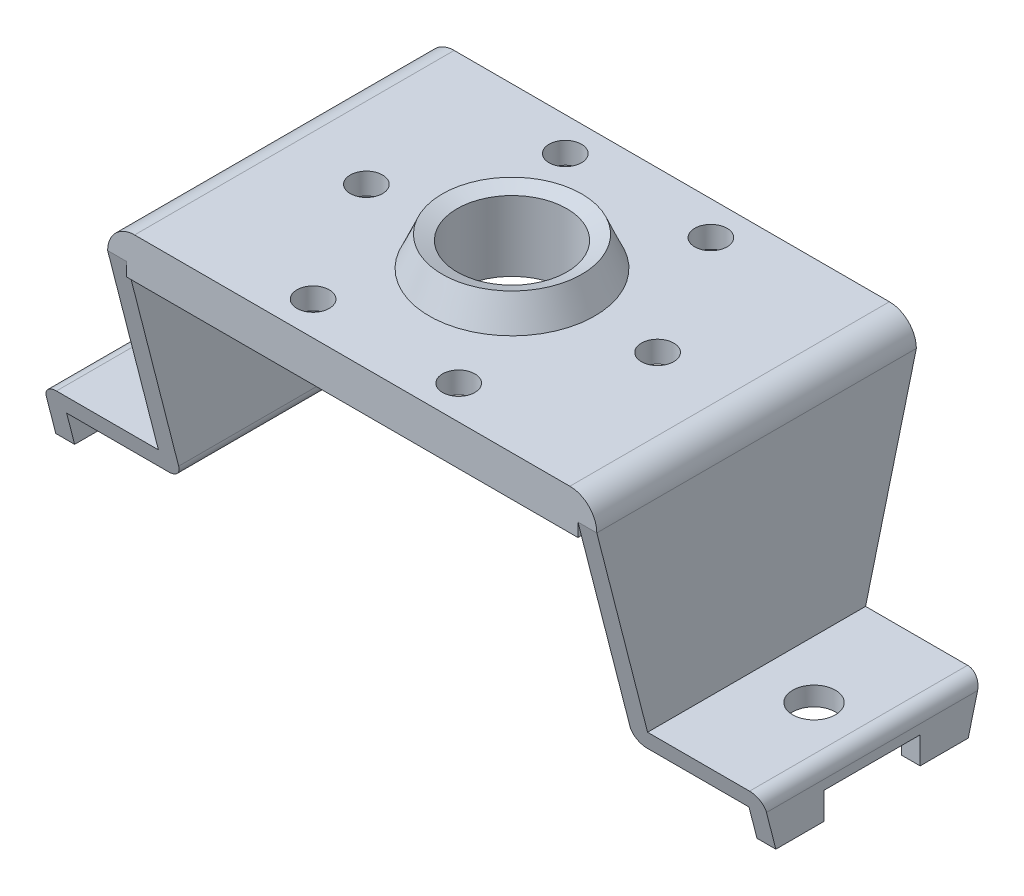
SolidWorks part; units mm, degrees
ref_plane "Front Plane" through (0, 0, 0) normal (0, 0, 1) x (1, 0, 0)
ref_plane "Top Plane" through (0, 0, 0) normal (0, 1, 0) x (1, 0, 0)
ref_plane "Right Plane" through (0, 0, 0) normal (1, 0, 0) x (0, 0, -1)
sketch "Sketch1" plane through (0, 0, 0) normal (0, 1, 0) x (1, 0, 0)
  line L1 (-17.9768, -15.0622) -> (17.9768, -15.0622)
  line L2 (-23.0568, -9.9822) -> (-23.0568, 9.9822)
  line L3 (-17.9768, 15.0622) -> (17.9768, 15.0622)
  line L4 (23.0569, -9.9822) -> (23.0569, 9.9822)
  line L5 (-23.0568, -15.0622) -> (23.0569, 15.0622) construction
  line L6 (-23.0568, 15.0622) -> (23.0569, -15.0622) construction
  arc A0 (-17.9768, -15.0622) -> (-23.0568, -9.9822) centre (-17.9768, -9.9822) cw
  arc A1 (17.9768, -15.0622) -> (23.0569, -9.9822) centre (17.9769, -9.9822) ccw
  arc A2 (17.9768, 15.0622) -> (23.0569, 9.9822) centre (17.9769, 9.9822) cw
  arc A3 (-23.0568, 9.9822) -> (-17.9768, 15.0622) centre (-17.9768, 9.9822) cw
  circle A4 centre (0, 0) radius 7.7978
  circle A5 centre (0, 0) radius 6.5722
  circle A6 centre (0, 0) radius 5.1752
  point P0 (0, 0)
  dimension "D3" = 5.08
  dimension "D4" = 15.5956
  dimension "D5" = 13.1445
  dimension "D6" = 10.3505
  dimension "D1" = 46.1137
  dimension "D2" = 30.1244
extrude "Boss-Extrude1" add sketch "Sketch1" against normal blind 2.032 contours A3 L2 A0 L1 A1 L4 A2 L3 A4 | A4 A5 | A5 A6
sketch "Sketch2" plane through (0, 0, 0) normal (1, 0, 0) x (0, 0, -1)
  line L0 (0, 0) -> (0, 6.6036) construction
  line L1 (0, 2.794) -> (-9.9655, 2.794) construction
  line L2 (-5.1752, 2.286) -> (-6.5722, 2.794)
  line L3 (-5.1752, 0) -> (-7.7978, 0)
  line L4 (0, 0) -> (-6.5722, 0) construction
  line L5 (-5.1752, 2.286) -> (-5.1752, 0)
  line L6 (-7.7978, 0) -> (-6.5722, 2.794)
  line L8 (0, 2.286) -> (-5.1752, 2.286) construction
  dimension "D1" = 2.794
  dimension "D2" = 7.7978
  dimension "D3" = 6.5722
  dimension "D4" = 5.1752
  dimension "D5" = 2.286
  dimension "D6" = 5.1752
revolve "Revolve1" add sketch "Sketch2" angle 360 about L0
sketch "Sketch3" plane through (0, 0, 0) normal (0, 0, 1) x (1, 0, 0)
  line L0 (0, 0) -> (0, -10.5163) construction
  line L1 (23.0569, 0) -> (23.0569, -25.6535) construction
  line L3 (0, 0) -> (23.0569, 0) construction
  line L4 (23.0569, -1.27) -> (23.0569, -21.209)
  line L5 (21.7868, 0) -> (21.2789, 0)
  line L6 (21.2789, 0) -> (21.2789, -21.717)
  line L7 (22.5489, -22.987) -> (23.0569, -22.987)
  line L8 (21.2789, -22.987) -> (32.1628, -22.987) construction
  line L9 (23.0569, -22.987) -> (32.1628, -22.987)
  line L10 (-32.1628, -25.9207) -> (-33.9408, -25.9207)
  line L11 (32.1628, -21.209) -> (23.0569, -21.209)
  line L12 (32.1628, -22.987) -> (32.1628, -25.9207)
  line L13 (32.1628, -25.9207) -> (33.9408, -25.9207)
  line L14 (33.9408, -25.9207) -> (33.9408, -22.479)
  line L15 (32.6708, -21.209) -> (32.1628, -21.209)
  line L16 (32.1628, -22.987) -> (32.1628, -25.9207)
  line L17 (32.1628, -22.987) -> (32.1628, -25.9207)
  line L18 (-32.1628, -22.987) -> (-32.1628, -25.9207)
  line L19 (-33.9408, -25.9207) -> (-33.9408, -22.479)
  line L20 (-32.6708, -21.209) -> (-32.1628, -21.209)
  line L21 (-22.5489, -22.987) -> (-23.0569, -22.987)
  line L22 (-23.0569, -22.987) -> (-32.1628, -22.987)
  line L23 (-32.1628, -21.209) -> (-23.0569, -21.209)
  line L24 (-23.0569, -1.27) -> (-23.0569, -21.209)
  line L25 (-21.7868, 0) -> (-21.2789, 0)
  line L26 (-21.2789, 0) -> (-21.2789, -21.717)
  arc A0 (33.9408, -22.479) -> (32.6708, -21.209) centre (32.6708, -22.479) ccw
  arc A1 (23.0569, -1.27) -> (21.7868, 0) centre (21.7869, -1.27) ccw
  arc A2 (21.2789, -21.717) -> (22.5489, -22.987) centre (22.5489, -21.717) ccw
  arc A3 (-33.9408, -22.479) -> (-32.6708, -21.209) centre (-32.6708, -22.479) cw
  arc A4 (-21.2789, -21.717) -> (-22.5489, -22.987) centre (-22.5489, -21.717) cw
  arc A5 (-23.0569, -1.27) -> (-21.7868, 0) centre (-21.7869, -1.27) cw
  point P17 (33.9408, -21.209)
  dimension "D8" = 1.27
  dimension "D1" = 22.987
  dimension "D2" = 1.778
  dimension "D3" = 10.8839
  dimension "D4" = 1.778
  dimension "D5" = 1.778
  dimension "D6" = 1.778
  dimension "D7" = 4.7117
extrude "Boss-Extrude2" add sketch "Sketch3" along normal up to surface and the other way up to surface contours A5 L24 L23 L20 A3 L19 L10 L18 L22 L21 A4 L26 L25 | L6 A2 L7 L9 L12 L13 L14 A0 L15 L11 L4 A1 L5 up to face at (0, -1.016, 15.0622) other way up to face at (0, -1.016, -15.0622)
sketch "Sketch4" plane through (0, 0, 15.0622) normal (0, 0, 1) x (1, 0, 0)
  line L0 (21.2789, 0) -> (-21.2789, 0)
  line L1 (-17.9768, 0) -> (17.9768, 0) construction
  line L2 (-21.2789, 0) -> (-23.0569, 0)
  line L3 (-23.0569, 0) -> (-23.0569, -2.032)
  line L4 (-23.0569, -1.27) -> (-23.0569, -21.209) construction
  line L5 (-23.0569, -2.032) -> (-21.2789, -2.032)
  line L6 (-21.2789, 0) -> (-21.2789, -21.717) construction
  line L7 (-21.2789, -2.032) -> (-17.9768, -2.032)
  line L8 (-17.9768, -2.032) -> (-17.9768, 0)
  line L9 (0, 0) -> (0, -5.6499) construction
  line L10 (17.9768, -2.032) -> (17.9768, 0)
  line L11 (21.2789, -2.032) -> (17.9768, -2.032)
  line L12 (23.0569, -2.032) -> (21.2789, -2.032)
  line L13 (21.2789, 0) -> (23.0569, 0)
  line L14 (23.0569, 0) -> (23.0569, -2.032)
  arc M8 (-21.7868, 0) -> (-23.0569, -1.27) centre (-21.7869, -1.27) ccw
  line M9 (-23.0569, -1.27) -> (-23.0569, -21.209)
  line M17 (-21.2789, -21.717) -> (-21.2789, 0)
  line M18 (-21.2789, 0) -> (-21.7868, 0)
  dimension "D1" = 1.778
extrude "Boss-Extrude3" add sketch "Sketch4" against normal up to surface (30.1244 mm away) contours L2 L3 M8 | L5 M9 M17 M18 M8 | L7 L8 L0 M17 | L14 L13 L0 L10 L11 L12 up to face at (0, -1.016, -15.0622)
fillet "Fillet1" radius 2.54 1 edges at (23.0569, 0, 0)
fillet "Fillet2" radius 2.54 1 edges at (-23.0569, 0, 0)
sketch "Sketch5" plane through (-33.9408, 0, 0) normal (-1, 0, 0) x (0, 0, 1)
  line L0 (0, 0) -> (0, -25.9207) construction
  line L1 (15.0622, -25.9207) -> (-15.0622, -25.9207) construction
  line L3 (-4.5339, -23.3807) -> (4.5339, -23.3807)
  line L4 (-4.5339, -23.3807) -> (-4.5339, -25.9207)
  line L5 (4.5339, -23.3807) -> (4.5339, -25.9207)
  line L6 (-4.5339, -25.9207) -> (4.5339, -25.9207)
  point P9 (0, -23.3807)
  dimension "D1" = 9.0678
  dimension "D2" = 2.54
  dimension "D3" = 4.5339
extrude "Cut-Extrude1" cut sketch "Sketch5" against normal blind 116.84
sketch "Sketch6" plane through (0, -21.209, 0) normal (0, 1, 0) x (1, 0, 0)
  line L0 (-32.6708, -15.0622) -> (-32.6708, 15.0622) construction
  line L1 (0, 0) -> (0, -33.0062) construction
  circle A0 centre (-28.4734, 0) radius 2.0129
  circle A1 centre (28.4734, 0) radius 2.0129
  point P4 (-32.6708, 0)
  dimension "D1" = 4.1974
  dimension "D2" = 4.0259
  dimension "D3" = 28.4734
extrude "Cut-Extrude2" cut sketch "Sketch6" against normal through all
sketch "Sketch7" plane through (0, 0, 0) normal (0, 1, 0) x (1, 0, 0)
  line L0 (0, 0) -> (0, -17.2763) construction
  line L1 (0, 0) -> (13.7258, 0) construction
  line L2 (0, 0) -> (-6.8629, -11.8869) construction
  circle A0 centre (13.7258, 0) radius 1.524
  circle A1 centre (-13.7258, 0) radius 1.524
  circle A2 centre (-6.8629, -11.8869) radius 1.524
  circle A3 centre (6.8629, 11.8869) radius 1.524
  circle A4 centre (-6.8629, 11.8869) radius 1.524
  circle A5 centre (6.8629, -11.8869) radius 1.524
  dimension "D2" = 3.048
  dimension "D1" = 13.7258
  dimension "D4" = 120
  dimension "D5" = 13.7258
  dimension "D6" = 13.7258
  dimension "D3" = 3
extrude "Cut-Extrude3" cut sketch "Sketch7" against normal through all
sketch "Sketch8" plane through (-23.0568, 0, 0) normal (-1, 0, 0) x (0, 0, 1)
  line L0 (0, -29.543) -> (0, 0) construction
  line L1 (0, -11.6475) -> (9.0678, -11.6475) construction
  line L2 (0, -11.6475) -> (-9.0678, -11.6475) construction
  line L3 (-9.0678, -11.6475) -> (-9.0678, -25.9207) construction
  line L4 (9.0678, -11.6475) -> (9.0678, -25.9207) construction
  line L5 (-4.5339, -25.9207) -> (-15.0622, -25.9207) construction
  line L6 (15.0622, -25.9207) -> (4.5339, -25.9207) construction
  line L7 (-15.0622, -2.54) -> (-9.0678, -25.9207)
  line L8 (9.0678, -25.9207) -> (15.0622, -2.54)
  line L9 (-15.0622, -2.54) -> (-15.0622, -25.9207)
  line L10 (-15.0622, -25.9207) -> (-9.0678, -25.9207)
  line L11 (9.0678, -25.9207) -> (15.0622, -25.9207)
  line L12 (15.0622, -25.9207) -> (15.0622, -2.54)
  point P11 (-9.798, -25.9207)
  point P15 (9.7981, -25.9207)
  dimension "D1" = 18.1356
  dimension "D2" = 11.6475
extrude "Cut-Extrude4" cut sketch "Sketch8" against normal blind 116.84 and the other way blind 116.84
ref_plane "Plane1" through (0, -1.016, 0) normal (0, 1, 0) x (1, 0, 0)
mirror "Mirror4" about plane through (0, -1.016, 0) normal (0, 1, 0) of "Revolve1"
sketch "Sketch9" plane through (0, -2.032, 0) normal (0, -1, 0) x (1, 0, 0)
  line L0 (-21.2789, 15.0622) -> (21.2789, 15.0622)
  line L1 (21.2789, 15.0622) -> (21.2789, -15.0622)
  line L2 (21.2789, -15.0622) -> (-21.2789, -15.0622)
  line L3 (-21.2789, -15.0622) -> (21.2789, -15.0622) construction
  line L4 (-21.2789, 15.0622) -> (-21.2789, -15.0622) construction
  line L5 (-21.2789, -15.0622) -> (-21.2789, 15.0622)
  line L6 (-19.5009, 13.2842) -> (19.5009, 13.2842)
  line L7 (19.5009, 13.2842) -> (19.5009, -13.2842)
  line L8 (19.5009, -13.2842) -> (-19.5009, -13.2842)
  line L9 (-19.5009, -13.2842) -> (-19.5009, 13.2842)
  dimension "D1" = 1.778
extrude "Boss-Extrude4" add sketch "Sketch9" along normal blind 1.778
